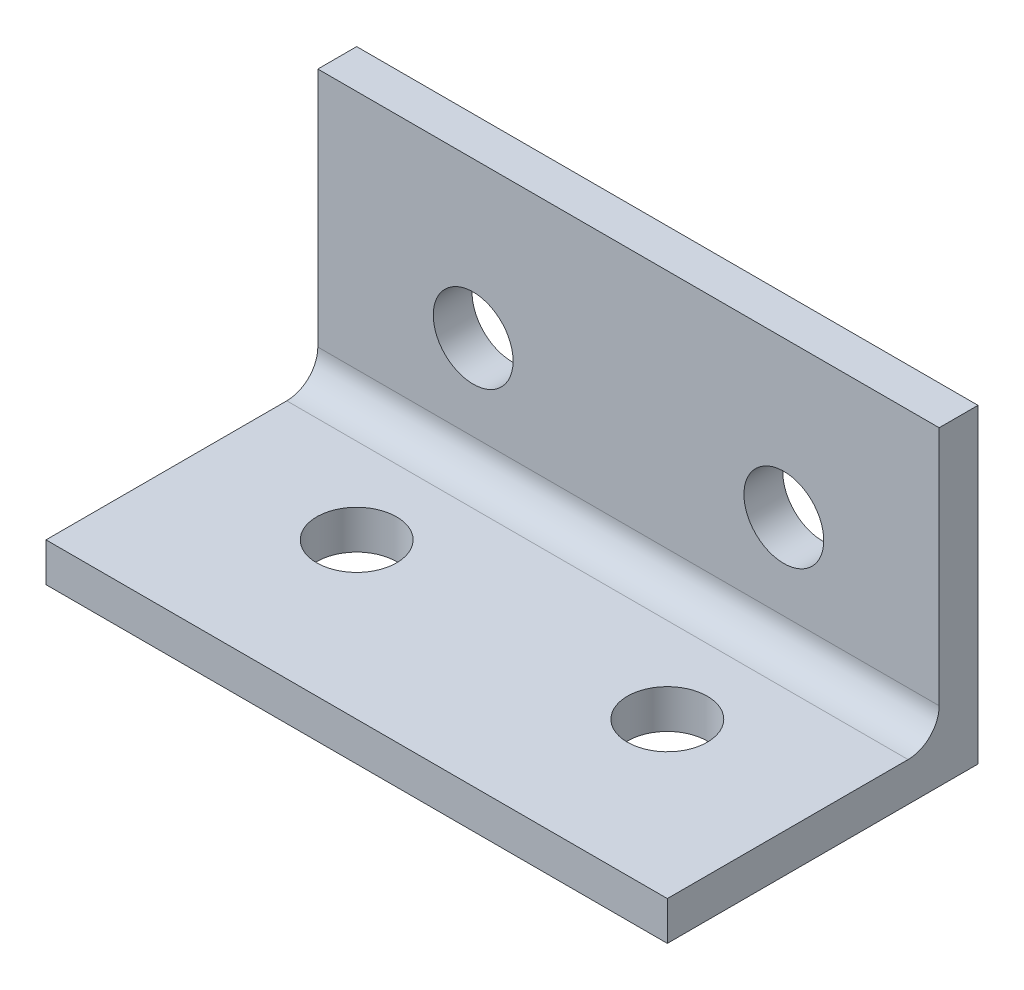
SolidWorks part; units mm, degrees
material "6061 Alloy"
ref_plane "Front Plane" through (0, 0, 0) normal (0, 0, 1) x (1, 0, 0)
ref_plane "Top Plane" through (0, 0, 0) normal (0, 1, 0) x (1, 0, 0)
ref_plane "Right Plane" through (0, 0, 0) normal (1, 0, 0) x (0, 0, -1)
sketch "Sketch1" plane through (0, 0, 0) normal (0, 1, 0) x (1, 0, 0)
  line L0 (0, 0) -> (0, 25.4)
  line L1 (0, 25.4) -> (50.8, 25.4)
  line L2 (50.8, 25.4) -> (50.8, 0)
  line L3 (50.8, 0) -> (0, 0)
  circle A0 centre (12.7, 12.7) radius 3.2639
  circle A1 centre (38.1, 12.7) radius 3.2639
  dimension "D3" = 12.7
  dimension "D7" = 6.5278
  dimension "D8" = 6.5278
  dimension "D1" = 50.8
  dimension "D2" = 25.4
  dimension "D4" = 12.7
  dimension "D5" = 12.7
  dimension "D6" = 12.7
extrude "Boss-Extrude1" add sketch "Sketch1" along normal blind 3.175
sketch "Sketch2" plane through (0, 3.175, 0) normal (0, 1, 0) x (1, 0, 0)
  line L0 (50.8, 0) -> (50.8, 25.4) construction
  line L1 (0, 25.4) -> (50.8, 25.4)
  line L2 (0, 25.4) -> (0, 22.225)
  line L3 (0, 22.225) -> (50.8, 22.225)
  line L4 (50.8, 25.4) -> (50.8, 22.225)
  dimension "D1" = 3.175
extrude "Boss-Extrude2" add sketch "Sketch2" along normal blind 22.225
sketch "Sketch3" plane through (0, 0, -22.225) normal (0, 0, 1) x (1, 0, 0)
  line L0 (0, 25.4) -> (50.8, 25.4) construction
  line L1 (0, 25.4) -> (0, 3.175) construction
  line L2 (50.8, 25.4) -> (50.8, 3.175) construction
  circle A0 centre (38.1, 12.7) radius 3.2639
  circle A1 centre (12.7, 12.7) radius 3.2639
  dimension "D5" = 6.5278
  dimension "D6" = 6.5278
  dimension "D1" = 12.7
  dimension "D2" = 12.7
  dimension "D3" = 12.7
  dimension "D4" = 12.7
extrude "Cut-Extrude1" cut sketch "Sketch3" against normal blind 22.225
fillet "Fillet1" radius 2.54 1 edges at (25.4, 3.175, -22.225)
